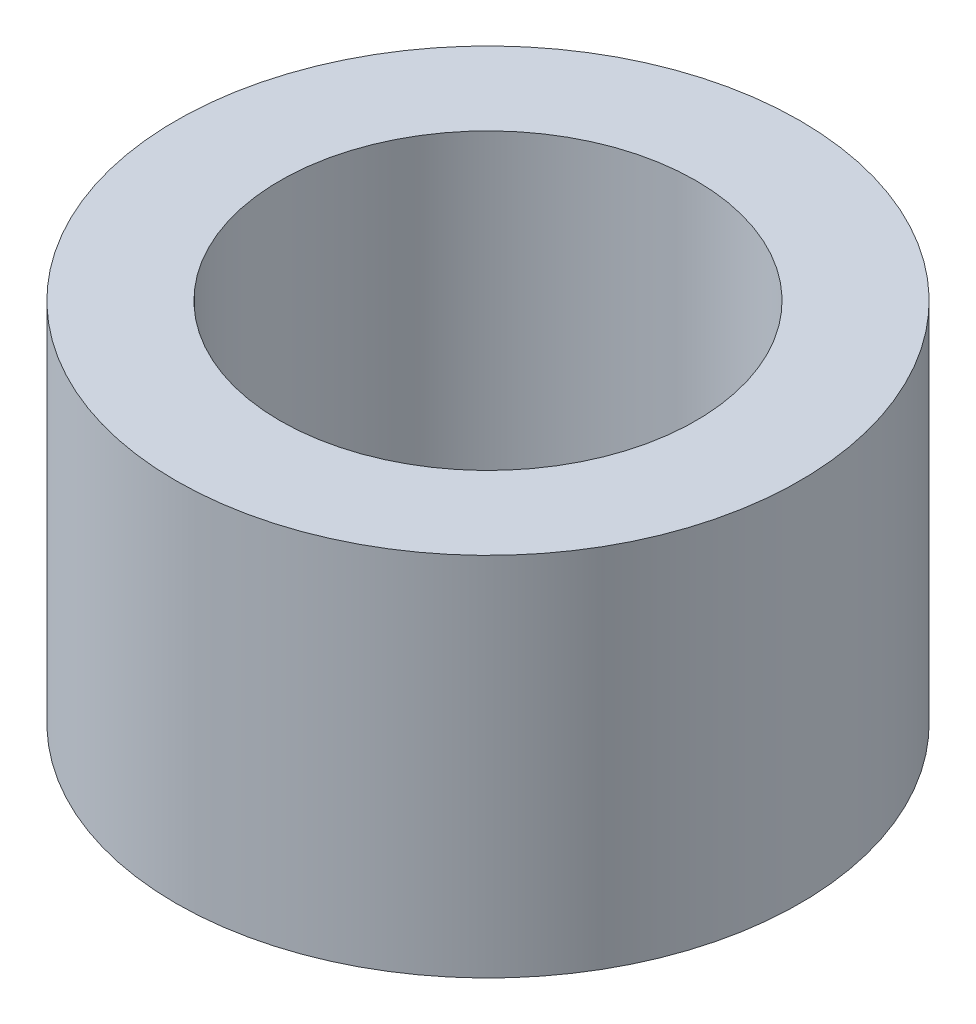
SolidWorks part; units mm, degrees
material "PVC Rigid"
ref_plane "Front Plane" through (0, 0, 0) normal (0, 0, 1) x (1, 0, 0)
ref_plane "Top Plane" through (0, 0, 0) normal (0, 1, 0) x (1, 0, 0)
ref_plane "Right Plane" through (0, 0, 0) normal (1, 0, 0) x (0, 0, -1)
sketch "Sketch1" plane through (0, 0, 0) normal (0, 1, 0) x (1, 0, 0)
  circle A0 centre (0, 0) radius 9.525
  circle A1 centre (0, 0) radius 6.35
  dimension "D1" = 19.05
  dimension "D2" = 12.7
extrude "Boss-Extrude1" add sketch "Sketch1" along normal blind 11.176
